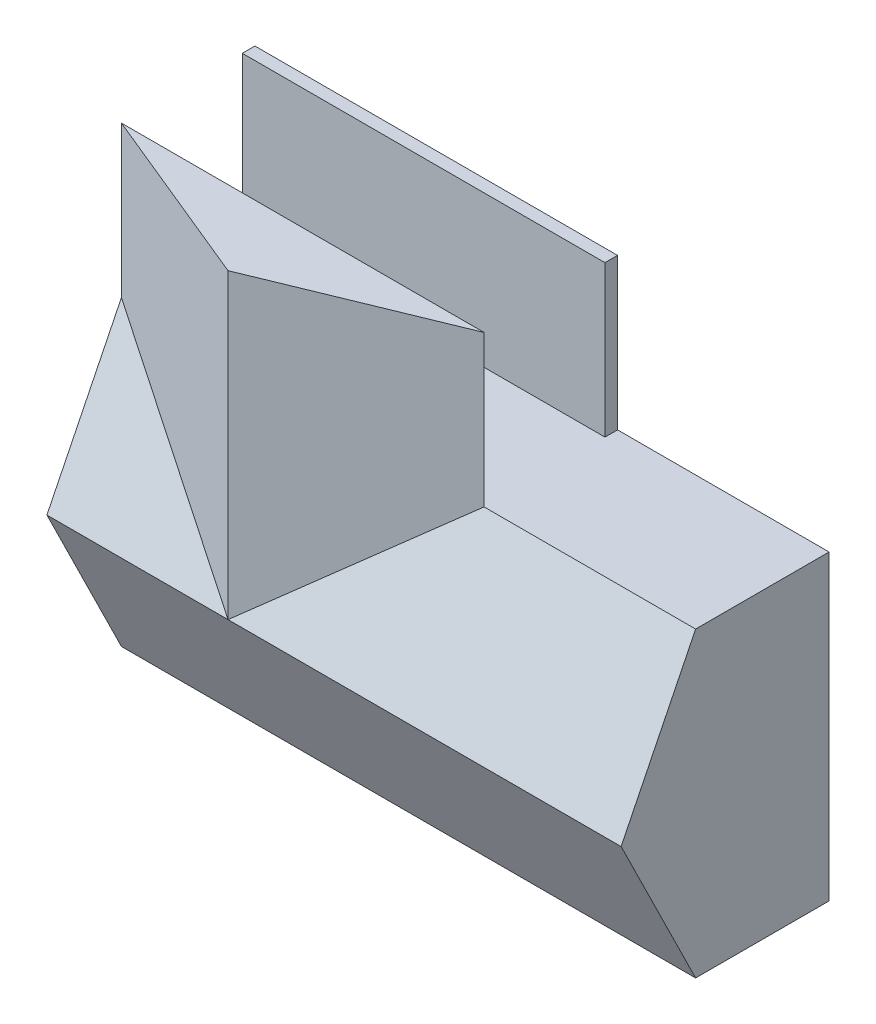
SolidWorks part; units mm, degrees
ref_plane "Front Plane" through (0, 0, 0) normal (0, 0, 1) x (1, 0, 0)
ref_plane "Top Plane" through (0, 0, 0) normal (0, 1, 0) x (1, 0, 0)
ref_plane "Right Plane" through (0, 0, 0) normal (1, 0, 0) x (0, 0, -1)
sketch "Sketch3" plane through (0, 0, 0) normal (0, 0, 1) x (1, 0, 0)
  line L0 (152.4, 152.4) -> (4550.005, 152.4)
  line L1 (0, 0) -> (11582.4, 0)
  line L2 (0, 0) -> (0, 6096)
  line L3 (0, 6096) -> (11582.4, 6096)
  line L4 (11582.4, 0) -> (11582.4, 6096)
  line L5 (4550.005, 152.4) -> (4550.005, 2596.7986)
  line L6 (4550.005, 2596.7986) -> (5842, 2596.7986)
  line L7 (11582.4, 6096) -> (7620, 6096) construction
  line L8 (7620, 6096) -> (5842, 6096) construction
  line L9 (5842, 5943.6) -> (5842, 3511.1986)
  line L10 (5943.6, 3511.1986) -> (10284.7543, 3511.1986)
  line L11 (7620, 5943.6) -> (7620, 3612.7986)
  line L12 (4550.005, 2596.7986) -> (5842, 2596.7986) construction
  line L13 (7315.2, 2495.1986) -> (7315.2, 152.4)
  line L14 (5842, 3511.1986) -> (5842, 2596.7986)
  line L15 (10386.3543, 3511.1986) -> (10386.3543, 2596.7986)
  line L16 (9786.5812, 3511.1986) -> (9786.5812, 2596.7986) construction
  line L17 (0, 6096) -> (0, 9448.8) construction
  line L18 (0, 9448.8) -> (6388.492, 9448.8) construction
  line L19 (6388.492, 9448.8) -> (6388.492, 6096) construction
  line L20 (11430, 152.4) -> (11430, 2495.1986)
  line L21 (3310.1163, 2590.8) -> (0, 2590.8) construction
  line L22 (152.4, 5943.6) -> (5842, 5943.6)
  line L23 (152.4, 152.4) -> (152.4, 5943.6)
  line L24 (4651.605, 152.4) -> (4651.605, 2495.1986)
  line L25 (4651.605, 2495.1986) -> (7315.2, 2495.1986)
  line L26 (7416.8, 2495.1986) -> (7416.8, 152.4)
  line L27 (10284.7543, 3511.1986) -> (10284.7543, 2596.7986)
  line L28 (5943.6, 3612.7986) -> (7620, 3612.7986)
  line L29 (5943.6, 5943.6) -> (5943.6, 3612.7986)
  line L30 (7721.6, 5943.6) -> (7721.6, 3612.7986)
  line L31 (7620, 6096) -> (7620, 3505.2) construction
  line L32 (7721.6, 6096) -> (7721.6, 3505.2) construction
  line L33 (5842, 6096) -> (5842, 3511.1986) construction
  line L34 (5943.6, 6096) -> (5943.6, 3511.1986) construction
  line L35 (5943.6, 5943.6) -> (7620, 5943.6)
  line L36 (152.4, 5943.6) -> (11430, 5943.6) construction
  line L37 (7721.6, 5943.6) -> (11430, 5943.6)
  line L38 (5842, 3612.7986) -> (11582.4, 3612.7986) construction
  line L39 (7721.6, 3612.7986) -> (11430, 3612.7986)
  line L40 (11430, 3612.7986) -> (11430, 5943.6)
  line L41 (11430, 152.4) -> (11430, 5943.6) construction
  line L42 (5842, 3511.1986) -> (11582.4, 3511.1986) construction
  line L43 (10386.3543, 3511.1986) -> (11430, 3511.1986)
  line L44 (10386.3543, 2596.7986) -> (11430, 2596.7986)
  line L45 (4550.005, 2596.7986) -> (11582.4, 2596.7986) construction
  line L46 (11430, 2596.7986) -> (11430, 3511.1986)
  line L47 (4651.605, 2495.1986) -> (11582.4, 2495.1986) construction
  line L48 (7315.2, 2596.7986) -> (7315.2, 0) construction
  line L49 (7416.8, 2596.7986) -> (7416.8, 0) construction
  line L50 (7416.8, 2495.1986) -> (11430, 2495.1986)
  line L51 (7416.8, 152.4) -> (11430, 152.4)
  line L52 (152.4, 152.4) -> (11430, 152.4) construction
  line L53 (4550.005, 0) -> (4550.005, 2596.7986) construction
  line L54 (4651.605, 0) -> (4651.605, 2495.1986) construction
  line L55 (4651.605, 152.4) -> (7315.2, 152.4)
  line L56 (5943.6, 3511.1986) -> (5943.6, 2596.7986)
  line L57 (5943.6, 2596.7986) -> (10284.7543, 2596.7986)
  line L58 (5943.6, 2596.7986) -> (7315.2, 2596.7986) construction
  dimension "D1" = 11582.4
  dimension "D2" = 6096
  dimension "D4" = 3962.4
  dimension "D5" = 1778
  dimension "D7" = 914.4
  dimension "D8" = 152.4
  dimension "D9" = 101.6
  dimension "D10" = 101.6
  dimension "D11" = 101.6
  dimension "D12" = 101.6
  dimension "D13" = 101.6
extrude "Boss-Extrude1" add sketch "Sketch3" along normal blind 2438.4 contours L1 L4 L3 L2 L55 L24 L25 L13 L51 L26 L50 L20 L46 L44 L15 L43 L40 L39 L30 L37 L10 L27 L6 L5 L0 L23 L22 L9 L29 L35 L11 L28
sketch "Sketch4" plane through (0, 0, 0) normal (0, 0, -1) x (-1, 0, 0)
  line L1 (-11582.4, 6096) -> (0, 6096)
  line L2 (-11582.4, 6096) -> (-11582.4, 0)
  line L3 (-11582.4, 0) -> (0, 0)
  line L4 (0, 6096) -> (0, 0)
extrude "Boss-Extrude2" add sketch "Sketch4" along normal blind 254
sketch "Sketch5" plane through (0, 0, 0) normal (0, 0, 1) x (1, 0, 0)
  line L1 (3330.805, 2596.7986) -> (152.4, 2596.7986)
  line L2 (152.4, 152.4) -> (152.4, 5943.6) construction
  line L3 (152.4, 2596.7986) -> (152.4, 2495.1986)
  line L4 (152.4, 152.4) -> (152.4, 5943.6) construction
  line L5 (152.4, 2495.1986) -> (3330.805, 2495.1986)
  line L6 (3330.805, 2495.1986) -> (3330.805, 2596.7986)
extrude "Boss-Extrude3" add sketch "Sketch5" along normal blind 1016
sketch "Sketch6" plane through (0, 0, 0) normal (-1, 0, 0) x (0, 0, 1)
  line L0 (2438.4, 6096) -> (2438.4, 0)
  line L1 (2438.4, 6096) -> (3941.5073, 3048)
  line L2 (2438.4, 3048) -> (3941.5073, 3048) construction
  line L3 (3941.5073, 3048) -> (2438.4, 0)
  dimension "D1" = 26.25
extrude "Boss-Extrude4" add sketch "Sketch6" against normal up to surface (11582.4 mm away) up to face at (11582.4, 3048, 1092.2)
sketch "Sketch7" plane through (0, 6096, 0) normal (0, 1, 0) x (1, 0, 0)
  line L0 (0, 254) -> (7315.2, 254) construction
  line L1 (0, 254) -> (11582.4, 254) construction
  line L2 (7315.2, 254) -> (7315.2, -2438.4) construction
  line L3 (0, -2438.4) -> (11582.4, -2438.4) construction
  line L4 (7937.8596, -2438.4) -> (5791.2, -3941.5073)
  line L5 (11582.4, -3941.5073) -> (0, -3941.5073) construction
  line L6 (5791.2, -3941.5073) -> (5791.2, -2438.4) construction
  line L7 (3644.5404, -2438.4) -> (5791.2, -3941.5073)
  line L8 (7937.8596, -2438.4) -> (3644.5404, -2438.4)
  dimension "D1" = 55
sketch "Sketch8" plane through (0, 0, -254) normal (0, 0, -1) x (-1, 0, 0)
  line L1 (0, 6096) -> (-7315.2, 6096)
  line L2 (0, 6096) -> (0, 9144)
  line L3 (0, 9144) -> (-7315.2, 9144)
  line L4 (-7315.2, 6096) -> (-7315.2, 9144)
  dimension "D1" = 7315.2
  dimension "D2" = 3048
extrude "Boss-Extrude6" add sketch "Sketch8" against normal blind 254 separate body
sketch "Sketch10" plane through (0, 9144, 0) normal (0, 1, 0) x (1, 0, 0)
  line L0 (7315.2, -2438.4) -> (0, -2438.4)
  line L1 (3644.5404, -2438.4) -> (3657.6, -4693.0609) construction
  line L2 (7315.2, -4693.0609) -> (0, -4693.0609) construction
  line L5 (0, -3941.5073) -> (4431.7653, -3941.5073) construction
  line L6 (11582.4, -3941.5073) -> (0, -3941.5073) construction
  line L7 (7315.2, -2438.4) -> (3653.2468, -3941.5073)
  line L8 (3653.2468, -3941.5073) -> (0, -2438.4)
extrude "Boss-Extrude9" add sketch "Sketch10" against normal up to surface (3048 mm away)
